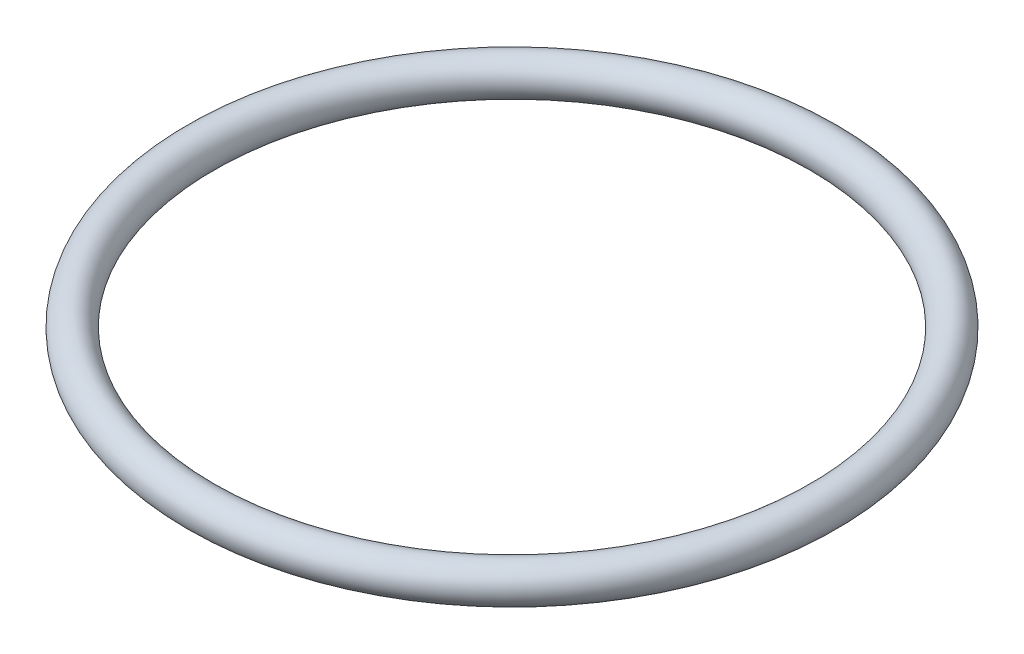
SolidWorks part; units mm, degrees
material "Rubber"
ref_plane "Front Plane" through (0, 0, 0) normal (0, 0, 1) x (1, 0, 0)
ref_plane "Top Plane" through (0, 0, 0) normal (0, 1, 0) x (1, 0, 0)
ref_plane "Right Plane" through (0, 0, 0) normal (1, 0, 0) x (0, 0, -1)
sketch "Sketch1" plane through (0, 0, 0) normal (0, 0, 1) x (1, 0, 0)
  line L0 (0, 0) -> (0, 4.6801) construction
  circle A0 centre (-43.5102, 0) radius 2.5908
  dimension "D1" = 5.1816
  dimension "D2" = 43.5102
revolve "Revolve1" add sketch "Sketch1" angle 360 about L0
